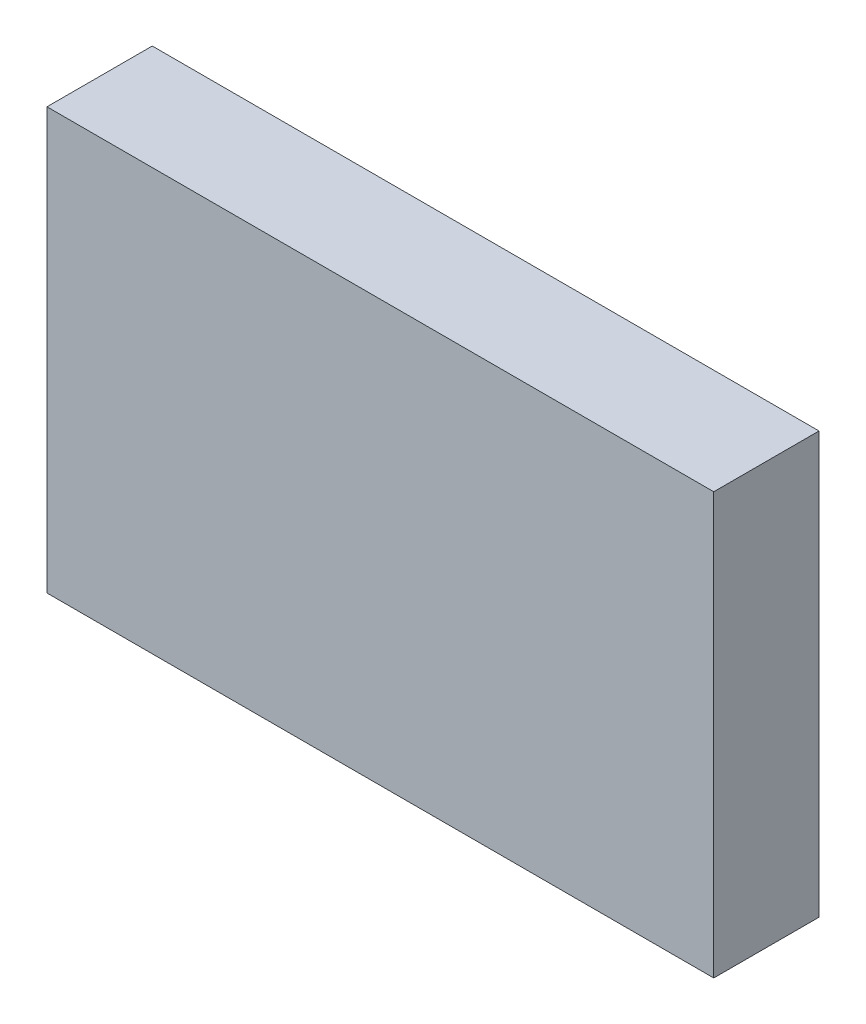
SolidWorks part; units mm, degrees
ref_plane "Alzado" through (0, 0, 0) normal (0, 0, 1) x (1, 0, 0)
ref_plane "Planta" through (0, 0, 0) normal (0, 1, 0) x (1, 0, 0)
ref_plane "Vista lateral" through (0, 0, 0) normal (1, 0, 0) x (0, 0, -1)
sketch "Croquis1" plane through (0, 0, 0) normal (0, 0, 1) x (1, 0, 0)
  line L1 (-47.5, 30) -> (47.5, 30)
  line L2 (-47.5, 30) -> (-47.5, -30)
  line L3 (-47.5, -30) -> (47.5, -30)
  line L4 (47.5, 30) -> (47.5, -30)
  line L5 (-47.5, 30) -> (47.5, -30) construction
  line L6 (-47.5, -30) -> (47.5, 30) construction
  point P0 (0, 0)
  dimension "D1" = 95
  dimension "D2" = 60
extrude "Saliente-Extruir1" add sketch "Croquis1" along normal blind 15 contours L2 L1 L4 L3
